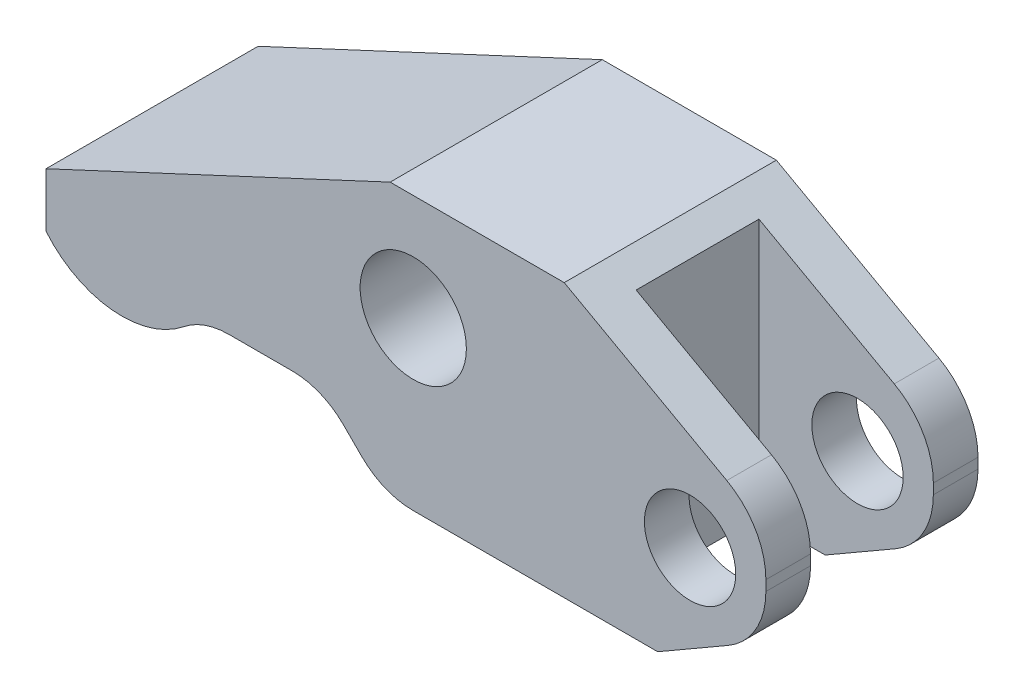
SolidWorks part; units mm, degrees
ref_plane "Front Plane" through (0, 0, 0) normal (0, 0, 1) x (1, 0, 0)
ref_plane "Top Plane" through (0, 0, 0) normal (0, 1, 0) x (1, 0, 0)
ref_plane "Right Plane" through (0, 0, 0) normal (1, 0, 0) x (0, 0, -1)
sketch "Sketch2" plane through (0, 0, 0) normal (0, 1, 0) x (1, 0, 0)
  line L0 (0, 0) -> (0, 26.0602) construction
  line L1 (0, 0) -> (34.3773, 0) construction
  line L3 (-23.749, 6.9977) -> (23.749, 6.9977)
  line L4 (-23.749, 6.9977) -> (-23.749, -6.9977)
  line L5 (-23.749, -6.9977) -> (23.749, -6.9977)
  line L6 (23.749, 6.9977) -> (23.749, -6.9977)
  point P10 (0, 6.9977)
  point P11 (23.749, 0)
  dimension "D1" = 47.498
  dimension "D2" = 13.9954
extrude "Boss-Extrude1" add sketch "Sketch2" along normal mid plane 18.0086
sketch "Sketch3" plane through (0, 0, 0) normal (0, 0, 1) x (1, 0, 0)
  line L0 (-23.749, -9.0043) -> (23.749, -9.0043) construction
  line L3 (23.749, 9.0043) -> (23.749, -9.0043) construction
  circle A0 centre (18.7452, -1.9939) radius 3.0124
  circle A1 centre (0.4826, 1.9939) radius 3.5052
  dimension "D5" = 7.0104
  dimension "D6" = 6.0249
  dimension "D1" = 7.0104
  dimension "D2" = 5.0038
  dimension "D3" = 3.9878
  dimension "D4" = 18.2626
extrude "Cut-Extrude1" cut sketch "Sketch3" against normal through all and the other way through all
sketch "Sketch5" plane through (0, 0, 0) normal (0, 0, 1) x (1, 0, 0)
  line L0 (16.6104, -9.0043) -> (21.2471, -6.3273)
  line L1 (-23.749, -9.0043) -> (23.749, -9.0043) construction
  line L2 (23.749, 9.0043) -> (23.749, -9.0043) construction
  line L3 (23.749, -1.9939) -> (23.749, -1.318)
  line L4 (21.1711, 3.0584) -> (10.4445, 9.0043)
  line L5 (-23.749, 9.0043) -> (23.749, 9.0043) construction
  line L6 (10.4445, 9.0043) -> (-1.0414, 9.0043)
  line L7 (-1.0414, 9.0043) -> (-23.749, -1.5844)
  line L8 (-23.749, 9.0043) -> (-23.749, -9.0043) construction
  line L9 (-23.749, -1.5844) -> (-23.749, -9.0043)
  line L10 (-23.749, -9.0043) -> (16.6104, -9.0043)
  arc A0 (23.749, -1.318) -> (21.1711, 3.0584) centre (18.7452, -1.318) ccw
  arc A1 (23.749, -1.9939) -> (21.2471, -6.3273) centre (18.7452, -1.9939) cw
  circle A2 centre (18.7452, -1.9939) radius 3.0124 construction
  point P18 (23.749, 1.6295)
  point P21 (23.749, -4.8828)
  dimension "D5" = 5.0038
  dimension "D6" = 13.3045
  dimension "D1" = 30
  dimension "D2" = 29
  dimension "D3" = 22.7076
  dimension "D4" = 25
extrude "Cut-Extrude2" cut sketch "Sketch5" against normal through all and the other way through all flip side to cut
sketch "Sketch6" plane through (0, 0, 0) normal (0, 0, 1) x (1, 0, 0)
  line L0 (-1.524, -9.0043) -> (-5.5118, -5.0165)
  line L1 (-23.749, -9.0043) -> (16.6104, -9.0043) construction
  line L2 (-5.5118, -5.0165) -> (-13.629, -5.0165)
  line L3 (-18.7452, -7.5057) -> (-23.749, -7.5057) construction
  line L4 (23.749, -1.318) -> (23.749, -1.9939) construction
  line L5 (-23.749, -5.1558) -> (-23.749, -9.0043)
  line L6 (-23.749, -1.5844) -> (-23.749, -9.0043) construction
  line L7 (-23.749, -9.0043) -> (-1.524, -9.0043)
  arc A0 (-23.749, -5.1558) -> (-13.629, -5.0165) centre (-18.7452, -1.0033) ccw
  circle A1 centre (0.4826, 1.9939) radius 3.5052 construction
  circle A3 centre (18.7452, -1.9939) radius 3.0124 construction
  dimension "D2" = 6.5024
  dimension "D4" = 45
  dimension "D5" = 5.9944
  dimension "D6" = 7.0104
  dimension "D1" = 5.5118
  dimension "D3" = 42.4942
extrude "Cut-Extrude3" cut sketch "Sketch6" against normal through all and the other way through all
fillet "Fillet1" radius 4.7752 3 edges at (-13.629, -5.0165, 0) (-5.5118, -5.0165, 0) (-1.524, -9.0043, 0)
sketch "Sketch7" plane through (0, 0, 0) normal (0, 1, 0) x (1, 0, 0)
  line L0 (23.749, 6.9977) -> (23.749, -6.9977) construction
  line L1 (23.749, 4.0513) -> (12.2428, 4.0513)
  line L2 (23.749, 4.0513) -> (23.749, -4.0513)
  line L3 (23.749, -4.0513) -> (12.2428, -4.0513)
  line L4 (12.2428, 4.0513) -> (12.2428, -4.0513)
  line L5 (-9.9047, 0) -> (9.9047, 0) construction
  point P6 (23.749, 0)
  dimension "D1" = 8.1026
  dimension "D2" = 11.5062
extrude "Cut-Extrude4" cut sketch "Sketch7" against normal through all and the other way through all
